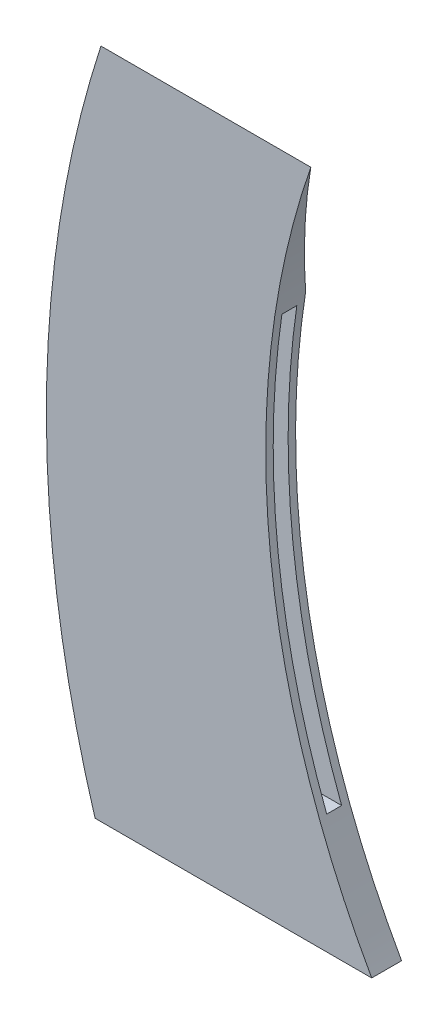
SolidWorks part; units mm, degrees
ref_plane "前视基准面" through (0, 0, 0) normal (0, 0, 1) x (1, 0, 0)
ref_plane "上视基准面" through (0, 0, 0) normal (0, 1, 0) x (1, 0, 0)
ref_plane "右视基准面" through (0, 0, 0) normal (1, 0, 0) x (0, 0, -1)
sketch "草图1" plane through (0, 0, 0) normal (0, 0, 1) x (1, 0, 0)
  line L1 (0, 0) -> (37.0629, 0)
  line L2 (0.7827, 90) -> (28.9034, 90)
  arc A3 (37.0629, 0) -> (28.9034, 90) centre (132.8649, 54.0553) cw
  arc A8 (0.7827, 90) -> (0, 0) centre (143.4763, 43.7557) ccw
  dimension "D6" = 28.1208
  dimension "D8" = 90
  dimension "D10" = 110
  dimension "D20" = 150
extrude "凸台-拉伸1" add sketch "草图1" along normal blind 4
sketch "草图2" plane through (0, 0, 0) normal (1, 0, 0) x (0, 0, -1)
  line L0 (-4, 90) -> (0, 90)
  line L1 (0, 90) -> (0, 71.1815)
  line L2 (-4, 90) -> (0, 71.1815)
  line L5 (0, 0) -> (0, 90) construction
  dimension "D1" = 12
extrude "切除-拉伸1" cut sketch "草图2" against normal through all and the other way through all
ref_plane "基准面1" through (0, 0, 2) normal (0, 0, -1) x (-1, 0, 0)
sketch "草图3" plane through (0, 0, 2) normal (0, 0, -1) x (-1, 0, 0)
  line L1 (-38, 15) -> (-8, 15)
  line L2 (-38, 15) -> (-38, 70)
  line L3 (-38, 70) -> (-8, 70)
  line L4 (-8, 15) -> (-8, 70)
  line L6 (-28.9034, 90) -> (-0.7827, 90) construction
  dimension "D1" = 20
  dimension "D2" = 55
  dimension "D3" = 8
  dimension "D4" = 30
extrude "切除-拉伸2" cut sketch "草图3" against normal mid plane 2
